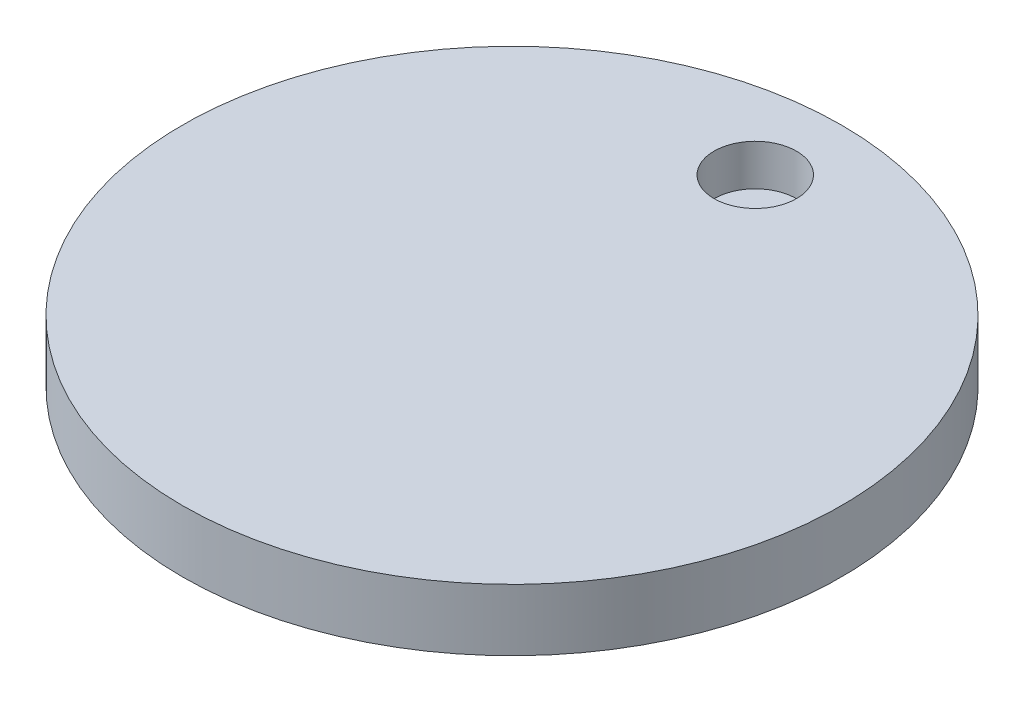
SolidWorks part; units mm, degrees
ref_plane "Front Plane" through (0, 0, 0) normal (0, 0, 1) x (1, 0, 0)
ref_plane "Top Plane" through (0, 0, 0) normal (0, 1, 0) x (1, 0, 0)
ref_plane "Right Plane" through (0, 0, 0) normal (1, 0, 0) x (0, 0, -1)
sketch "Sketch1" plane through (0, 0, 0) normal (0, 1, 0) x (1, 0, 0)
  circle A0 centre (0, 0) radius 101.6
  dimension "D1" = 203.2
extrude "Boss-Extrude1" add sketch "Sketch1" along normal blind 19.05
sketch "Sketch2" plane through (0, 19.05, 0) normal (0, 1, 0) x (1, 0, 0)
  circle A0 centre (0, 75) radius 12.7
  dimension "D1" = 25.4
  dimension "D2" = 75
extrude "Cut-Extrude1" cut sketch "Sketch2" against normal blind 12.7
